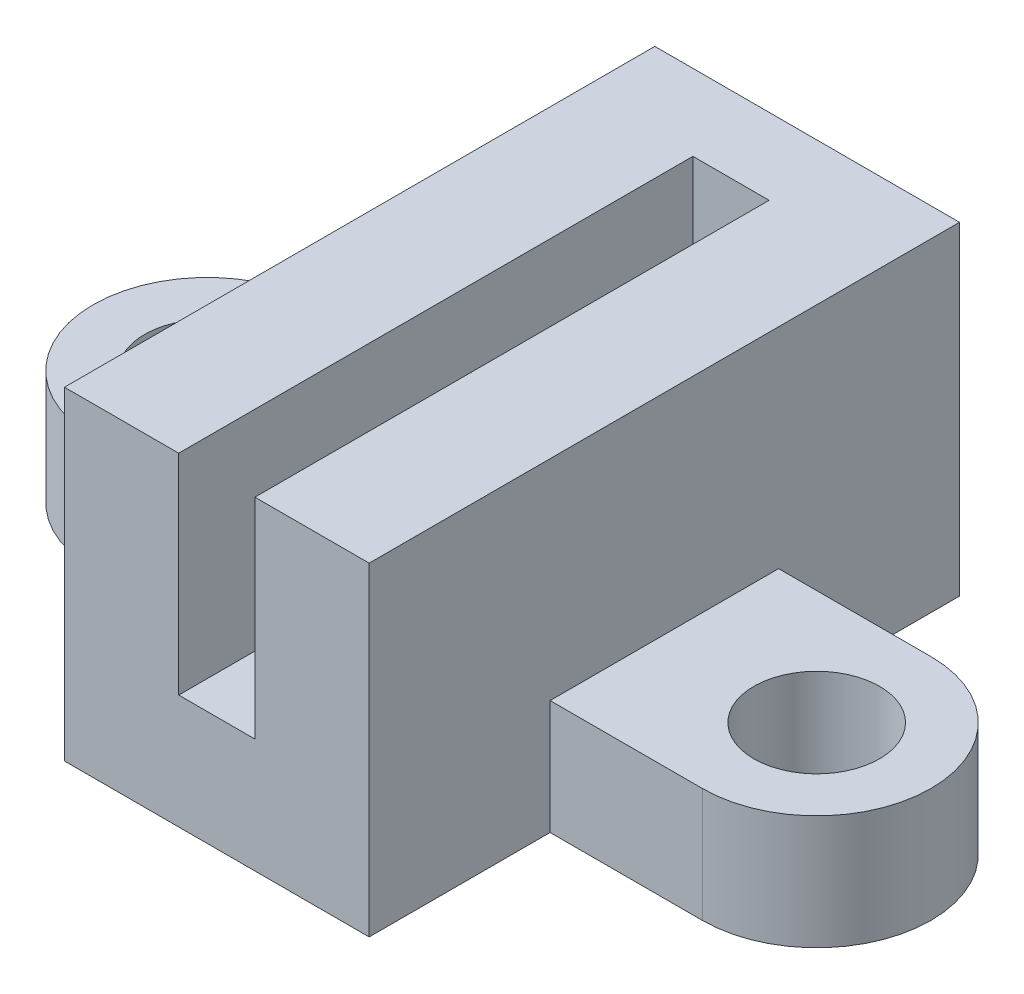
SolidWorks part; units mm, degrees
ref_plane "Front Plane" through (0, 0, 0) normal (0, 0, 1) x (1, 0, 0)
ref_plane "Top Plane" through (0, 0, 0) normal (0, 1, 0) x (1, 0, 0)
ref_plane "Right Plane" through (0, 0, 0) normal (1, 0, 0) x (0, 0, -1)
sketch "Sketch1" plane through (0, 0, 0) normal (0, 0, 1) x (1, 0, 0)
  line L0 (0, 0) -> (0, 8.5)
  line L1 (0, 8.5) -> (3, 8.5)
  line L2 (3, 8.5) -> (3, 3)
  line L3 (3, 3) -> (5, 3)
  line L4 (5, 3) -> (5, 8.5)
  line L5 (5, 8.5) -> (8, 8.5)
  line L6 (8, 8.5) -> (8, 0)
  line L7 (8, 0) -> (0, 0)
  dimension "D1" = 2
  dimension "D2" = 5.5
  dimension "D3" = 3
  dimension "D4" = 3
  dimension "D5" = 3
extrude "Boss-Extrude1" add sketch "Sketch1" along normal blind 13.5
sketch "Sketch2" plane through (0, 0, 0) normal (0, 0, -1) x (-1, 0, 0)
  line L1 (-8, 0) -> (0, 0)
  line L2 (-8, 0) -> (-8, 8.5)
  line L3 (-8, 8.5) -> (0, 8.5)
  line L4 (0, 0) -> (0, 8.5)
extrude "Boss-Extrude2" add sketch "Sketch2" along normal blind 2
sketch "Sketch3" plane through (0, 0, 0) normal (0, 1, 0) x (1, 0, 0)
  line L0 (0, -5.75) -> (8, -5.75) construction
  line L1 (0, -13.5) -> (0, 2) construction
  line L2 (8, -13.5) -> (8, 2) construction
  line L3 (0, -2.75) -> (-4, -2.75)
  line L4 (-4, -8.75) -> (0, -8.75)
  line L5 (8, -2.75) -> (12, -2.75)
  line L6 (12, -8.75) -> (8, -8.75)
  line L7 (0, -2.75) -> (0, -8.75)
  line L8 (8, -8.75) -> (8, -2.75)
  arc A0 (-4, -2.75) -> (-4, -8.75) centre (-4, -5.75) ccw
  arc A1 (12, -2.75) -> (12, -8.75) centre (12, -5.75) cw
  circle A2 centre (-4, -5.75) radius 1.65
  circle A3 centre (12, -5.75) radius 1.65
  dimension "D1" = 4
  dimension "D2" = 3
  dimension "D3" = 3.3
  dimension "D4" = 3.3
extrude "Boss-Extrude3" add sketch "Sketch3" along normal blind 3
